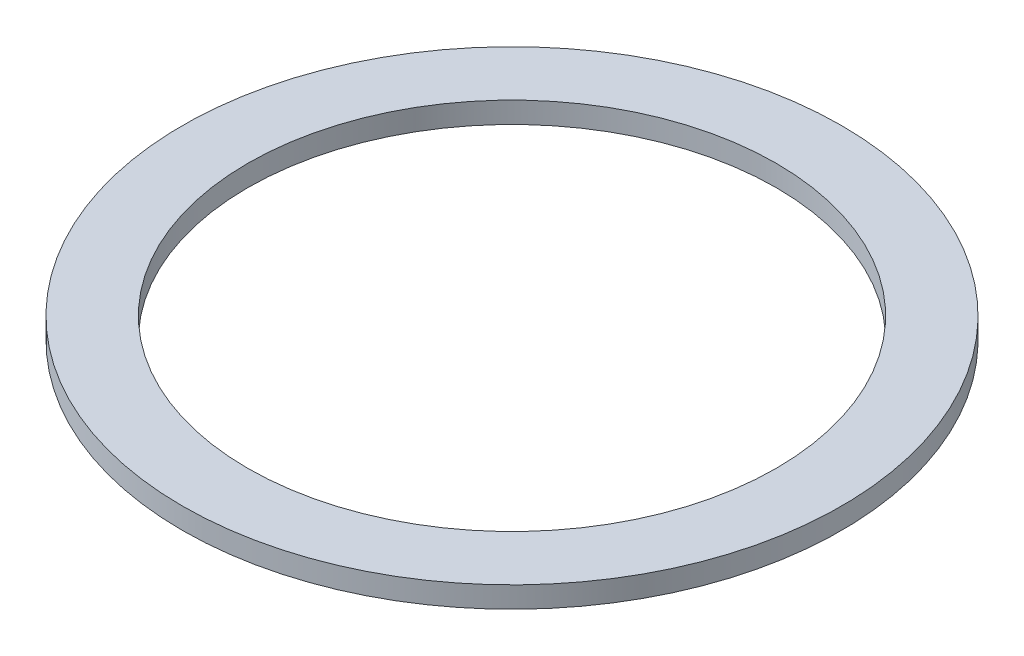
SolidWorks part; units mm, degrees
material "A-Glass Fiber"
ref_plane "Front Plane" through (0, 0, 0) normal (0, 0, 1) x (1, 0, 0)
ref_plane "Top Plane" through (0, 0, 0) normal (0, 1, 0) x (1, 0, 0)
ref_plane "Right Plane" through (0, 0, 0) normal (1, 0, 0) x (0, 0, -1)
sketch "Sketch1" plane through (0, 0, 0) normal (0, 1, 0) x (1, 0, 0)
  circle A0 centre (0, 0) radius 39.6875
  circle A2 centre (0, 0) radius 49.5046
  dimension "D1" = 79.375
  dimension "D2" = 99.0092
extrude "Boss-Extrude1" add sketch "Sketch1" along normal blind 3.175
